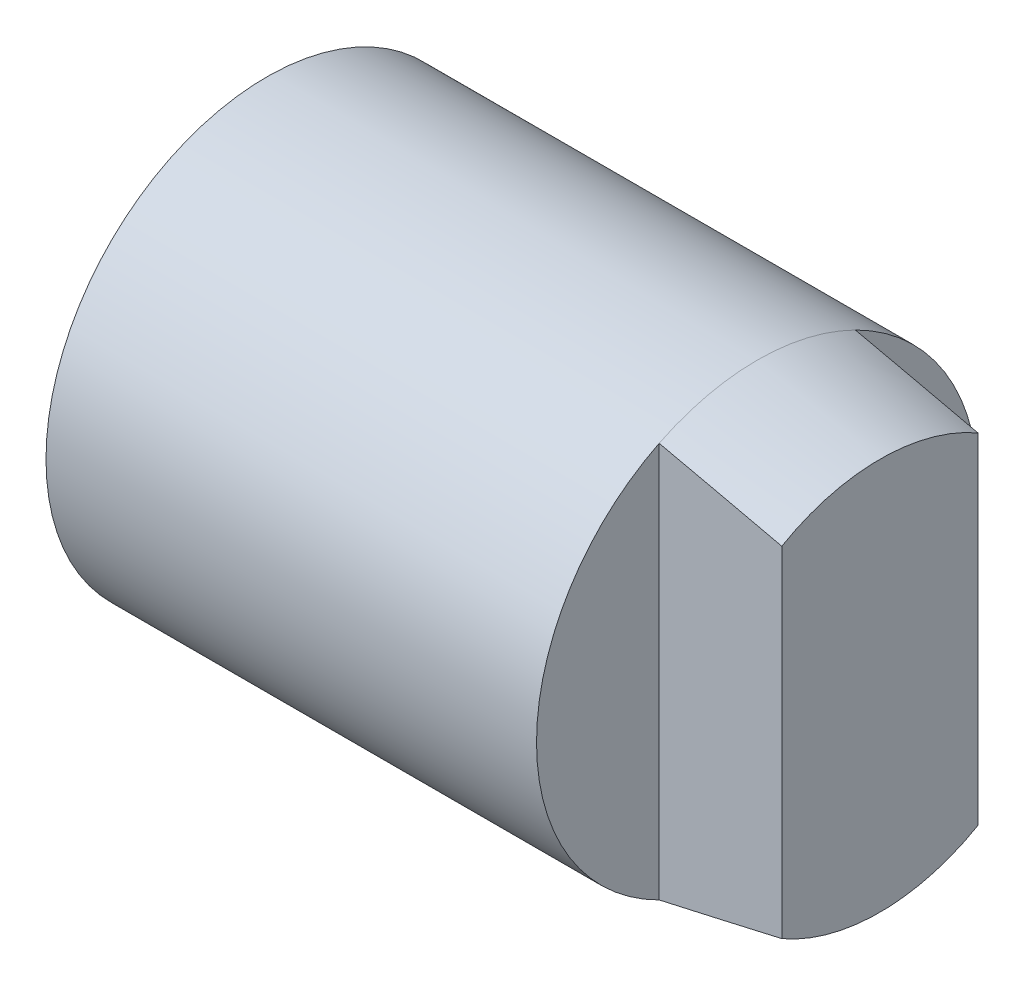
SolidWorks part; units mm, degrees
ref_plane "Front Plane" through (0, 0, 0) normal (0, 0, 1) x (1, 0, 0)
ref_plane "Top Plane" through (0, 0, 0) normal (0, 1, 0) x (1, 0, 0)
ref_plane "Right Plane" through (0, 0, 0) normal (1, 0, 0) x (0, 0, -1)
sketch "Sketch1" plane through (0, 0, 0) normal (0, 1, 0) x (1, 0, 0)
  line L0 (0, 0) -> (12.5, 0)
  line L1 (12.5, 0) -> (12.5, 4)
  line L2 (12.5, 4) -> (10, 4.5)
  line L3 (10, 4.5) -> (0, 4.5)
  line L4 (0, 4.5) -> (0, 0)
  dimension "D1" = 10
  dimension "D2" = 4.5
  dimension "D3" = 4
  dimension "D4" = 2.5
revolve "Revolve1" add sketch "Sketch1" angle 360 about L0
sketch "Sketch2" plane through (12.5, 0, 0) normal (1, 0, 0) x (0, 0, -1)
  line L0 (-2, -4.0311) -> (-2, 4.0311)
  line L1 (2, -4.0311) -> (2, 4.0311)
  circle A0 centre (0, 0) radius 4.5 construction
  arc A1 (-2, 4.0311) -> (-2, -4.0311) centre (0, 0) ccw
  arc A2 (2, -4.0311) -> (2, 4.0311) centre (0, 0) ccw
  dimension "D1" = 4
extrude "Cut-Extrude1" cut sketch "Sketch2" against normal blind 2.5
